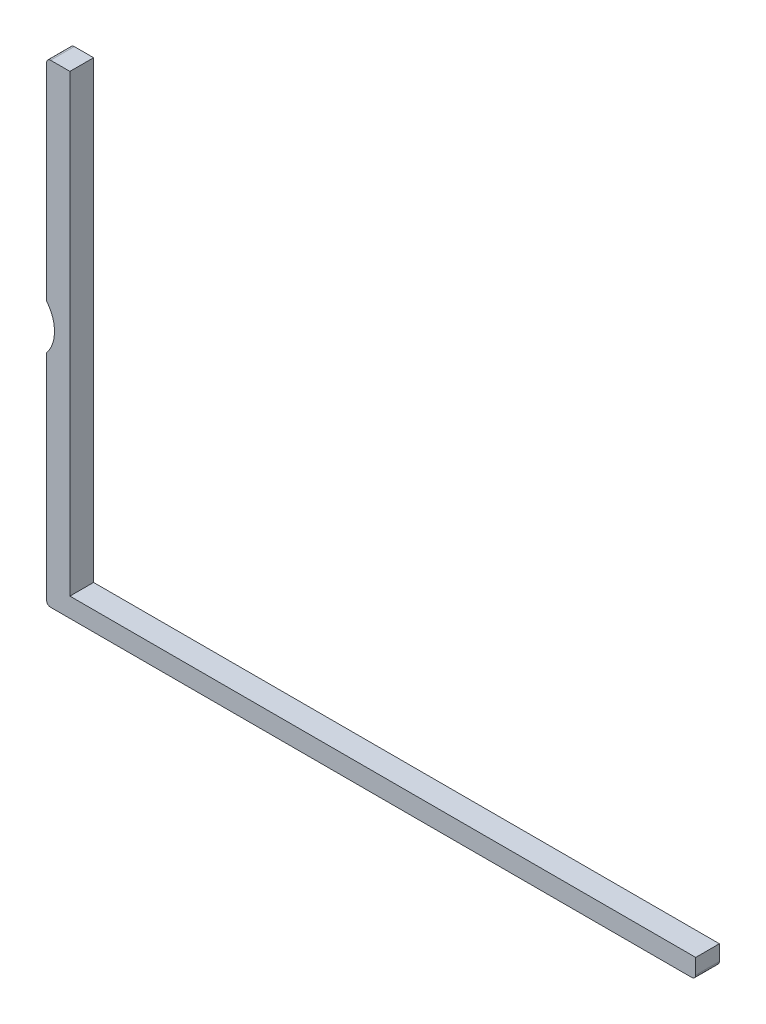
SolidWorks part; units mm, degrees
material "acero"
ref_plane "Alzado" through (0, 0, 0) normal (0, 0, 1) x (1, 0, 0)
ref_plane "Planta" through (0, 0, 0) normal (0, 1, 0) x (1, 0, 0)
ref_plane "Vista lateral" through (0, 0, 0) normal (1, 0, 0) x (0, 0, -1)
sketch "Croquis1" plane through (0, 0, 0) normal (0, 0, 1) x (1, 0, 0)
  line L0 (0, 0) -> (82.2, 0)
  line L1 (82.2, 0) -> (82.2, 2.45)
  line L2 (82.2, 2.45) -> (2.95, 2.45)
  line L3 (2.95, 2.45) -> (2.95, 60)
  line L4 (2.95, 60) -> (0, 60)
  line L5 (0, 60) -> (0, 33.3284)
  line L6 (0, 27.6716) -> (0, 0)
  arc A0 (0, 27.6716) -> (0, 33.3284) centre (-3.5, 30.5) ccw
  dimension "D3" = 9
  dimension "D1" = 3.5
  dimension "D2" = 30.5
  dimension "D4" = 2.45
  dimension "D5" = 82.2
  dimension "D6" = 2.95
  dimension "D7" = 60
extrude "Saliente-Extruir1" add sketch "Croquis1" along normal blind 3
fillet "Redondeo1" radius 0.5 3 edges at (82.2, 0, 1.5) (0, 0, 1.5) (0, 60, 1.5)
equation "\"D4@Croquis1\"=3.25-0.8"
equation "\"D7@Croquis1\"=60.00mm"
equation "\"D2@Croquis1\"=30.00mm+0.5"
